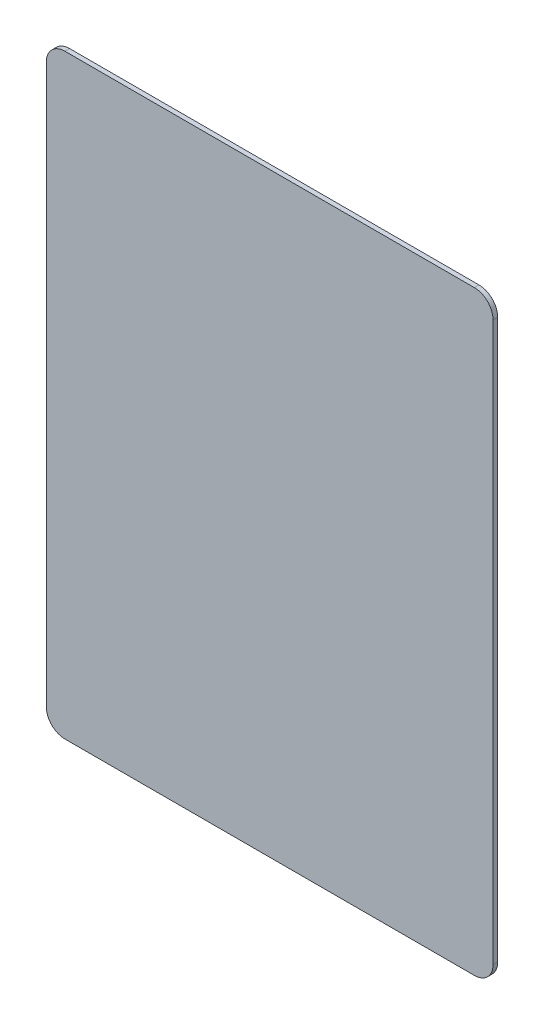
SolidWorks part; units mm, degrees
ref_plane "Front Plane" through (0, 0, 0) normal (0, 0, 1) x (1, 0, 0)
ref_plane "Top Plane" through (0, 0, 0) normal (0, 1, 0) x (1, 0, 0)
ref_plane "Right Plane" through (0, 0, 0) normal (1, 0, 0) x (0, 0, -1)
sketch "Sketch1" plane through (0, 0, 0) normal (0, 0, 1) x (1, 0, 0)
  line L1 (-47.487, 164.1337) -> (92.213, 164.1337)
  line L2 (-53.837, 157.7837) -> (-53.837, -32.7163)
  line L3 (-47.487, -39.0663) -> (92.213, -39.0663)
  line L4 (98.563, 157.7837) -> (98.563, -32.7163)
  arc A0 (-47.487, 164.1337) -> (-53.837, 157.7837) centre (-47.487, 157.7837) ccw
  arc A1 (92.213, 164.1337) -> (98.563, 157.7837) centre (92.213, 157.7837) cw
  arc A2 (92.213, -39.0663) -> (98.563, -32.7163) centre (92.213, -32.7163) ccw
  arc A3 (-53.837, -32.7163) -> (-47.487, -39.0663) centre (-47.487, -32.7163) ccw
  point P6 (-53.837, 164.1337)
  point P11 (98.563, -39.0663)
  point P14 (-53.837, -39.0663)
  dimension "D3" = 6.35
  dimension "D1" = 152.4
  dimension "D2" = 203.2
extrude "Boss-Extrude1" add sketch "Sketch1" along normal blind 1.5875
